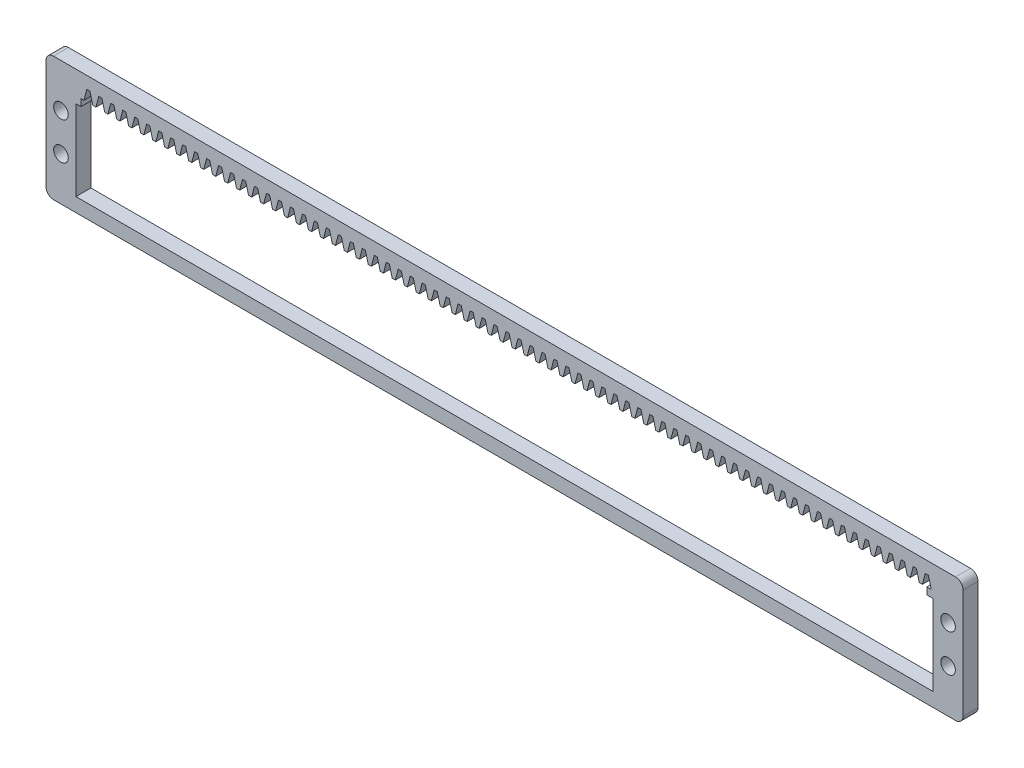
SolidWorks part; units mm, degrees
other "Markup1"
sketch "Sketch6" plane through (0, -30, 3.6) normal (0, 0, 1) x (1, 0, 0)
other "Markup2"
sketch "Sketch7" plane through (0, -30, 3.6) normal (0, 0, 1) x (1, 0, 0)
ref_plane "Front Plane" through (0, 0, 0) normal (0, 0, 1) x (1, 0, 0)
ref_plane "Top Plane" through (0, 0, 0) normal (0, 1, 0) x (1, 0, 0)
ref_plane "Right Plane" through (0, 0, 0) normal (1, 0, 0) x (0, 0, -1)
sketch "Sketch1" plane through (0, 0, 0) normal (0, 0, 1) x (1, 0, 0)
  line L1 (2, 0) -> (243, 0)
  line L2 (0, -2) -> (0, -31.22)
  line L3 (2, -33.22) -> (243, -33.22)
  line L4 (245, -2) -> (245, -31.22)
  arc A0 (243, -33.22) -> (245, -31.22) centre (243, -31.22) ccw
  arc A1 (0, -31.22) -> (2, -33.22) centre (2, -31.22) ccw
  arc A2 (2, 0) -> (0, -2) centre (2, -2) ccw
  arc A3 (243, 0) -> (245, -2) centre (243, -2) cw
  point P7 (245, -33.22)
  point P12 (0, 0)
  point P15 (245, 0)
  dimension "D3" = 2
  dimension "D1" = 33.22
  dimension "D2" = 245
extrude "Boss-Extrude1" add sketch "Sketch1" along normal blind 4
sketch "Sketch2" plane through (0, 0, 4) normal (0, 0, 1) x (1, 0, 0)
  line L0 (2, -33.22) -> (243, -33.22) construction
  line L1 (8, -8) -> (237, -8)
  line L2 (8, -8) -> (8, -29.5)
  line L3 (8, -29.5) -> (237, -29.5)
  line L4 (237, -8) -> (237, -29.5)
  line L5 (0, -2) -> (0, -31.22) construction
  line L7 (245, -31.22) -> (245, -2) construction
  line L8 (8, -18.75) -> (237, -18.75) construction
  line L12 (8, -29.5) -> (237, -29.5) construction
  line L13 (237, -4.3144) -> (237, -29.5) construction
  dimension "D1" = 21.5
  dimension "D2" = 8
  dimension "D3" = 8
  dimension "D4" = 3.72
extrude "Cut-Extrude1" cut sketch "Sketch2" against normal through all
sketch "Sketch3" plane through (0, 0, 4) normal (0, 0, 1) x (1, 0, 0)
  line L0 (237, -8) -> (8, -8) construction
  line L1 (9.35, -8) -> (235.32, -8)
  line L2 (9.35, -8) -> (9.35, -6.15)
  line L3 (9.35, -6.15) -> (235.32, -6.15)
  line L4 (235.32, -8) -> (235.32, -6.15)
  line L5 (237, -29.5) -> (237, -8) construction
  line L6 (8, -8) -> (8, -29.5) construction
  dimension "D1" = 1.85
  dimension "D2" = 1.68
  dimension "D3" = 1.35
extrude "Cut-Extrude2" cut sketch "Sketch3" against normal through all
sketch "Sketch4" plane through (0, 0, 4) normal (0, 0, 1) x (1, 0, 0)
  line L0 (237.7, -6.15) -> (236.5, -6.15) construction
  line L1 (235.32, -6.15) -> (9.35, -6.15) construction
  line L2 (237.7, -6.15) -> (238.465, -3.2492) construction
  line L3 (238.465, -3.2492) -> (235.735, -3.2492) construction
  line L4 (235.735, -3.2492) -> (236.5, -6.15)
  line L5 (235.735, -3.2492) -> (234.905, -3.2492)
  line L6 (234.905, -3.2492) -> (234.14, -6.15)
  line L7 (234.14, -6.15) -> (236.5, -6.15)
  line L10 (236.5, -6.15) -> (237.7, -6.15) construction
  dimension "D1" = 1.2
  dimension "D3" = 3
  dimension "D4" = 0.83
  dimension "D5" = 2.73
extrude "Cut-Extrude4" cut sketch "Sketch4" against normal through all
pattern_linear "LPattern1" count 71 spacing 3.2 along (-1, 0, 0) of "Cut-Extrude4"
sketch "Sketch5" plane through (0, 0, 4) normal (0, 0, 1) x (1, 0, 0)
  line L0 (237, -16.61) -> (245, -16.61) construction
  line L1 (243, 0) -> (2, 0) construction
  line L2 (8, -8) -> (8, -29.5) construction
  line L3 (0, -2) -> (0, -31.22) construction
  line L4 (2, -33.22) -> (243, -33.22) construction
  line L5 (0, -16.61) -> (8, -16.61) construction
  line L7 (241, -11.61) -> (241, -21.61) construction
  line L8 (4, -11.61) -> (4, -21.61) construction
  line L9 (237, -29.5) -> (237, -8) construction
  line L10 (245, -31.22) -> (245, -2) construction
  circle A4 centre (4, -11.61) radius 1.95
  circle A5 centre (4, -21.61) radius 1.95
  circle A6 centre (241, -11.61) radius 1.95
  circle A7 centre (241, -21.61) radius 1.95
  point P8 (241, -16.61)
  point P18 (4, -16.61)
  point P22 (4, -16.61)
  point P31 (241, -16.61)
  dimension "D1" = 3.9
  dimension "D3" = 3.9
  dimension "D4" = 3.9
  dimension "D6" = 3.9
  dimension "D5" = 10
  dimension "D7" = 10
extrude "Cut-Extrude5" cut sketch "Sketch5" against normal blind 10
